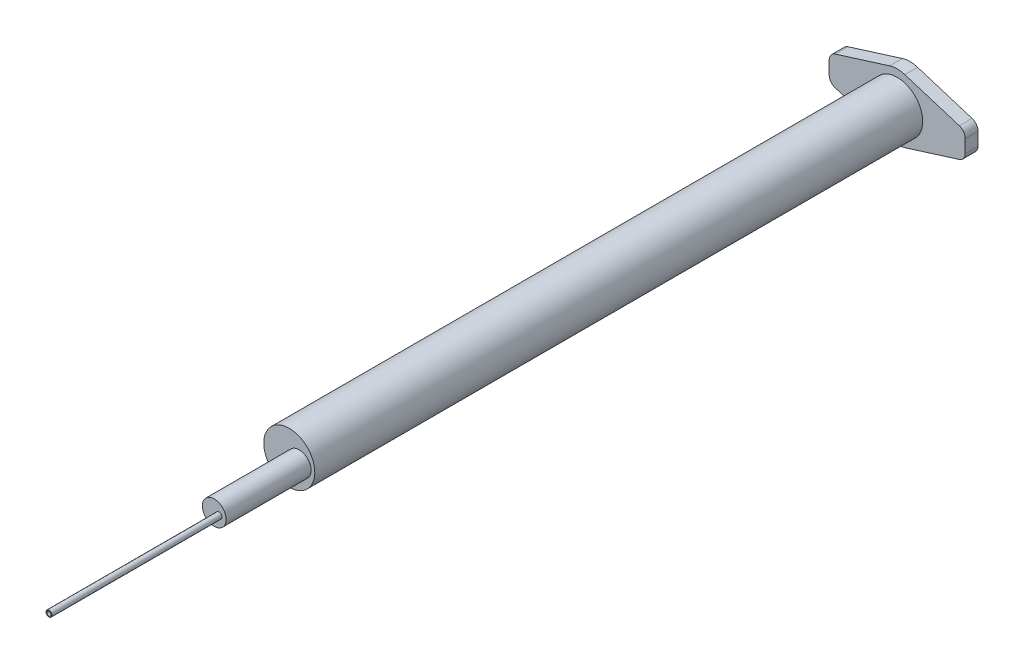
SolidWorks part; units mm, degrees
ref_plane "Front" through (0, 0, 0) normal (0, 0, 1) x (1, 0, 0)
ref_plane "Top" through (0, 0, 0) normal (0, 1, 0) x (1, 0, 0)
ref_plane "Right" through (0, 0, 0) normal (1, 0, 0) x (0, 0, -1)
sketch "草图1" plane through (0, 0, 0) normal (0, 0, 1) x (1, 0, 0)
  circle A0 centre (0, 0) radius 3
  circle A1 centre (0, 0) radius 2.5
extrude "凸台-拉伸1" add sketch "草图1" along normal blind 71.5
sketch "草图2" plane through (0, 0, 71.5) normal (0, 0, 1) x (1, 0, 0)
  circle A0 centre (0, 0) radius 3
  circle A1 centre (1.174, 0) radius 1
  point P5 (1.174, 0)
extrude "凸台-拉伸2" add sketch "草图2" against normal blind 1
sketch "草图3" plane through (0, 0, 0) normal (0, 0, -1) x (-1, 0, 0)
  line L6 (7.2983, -1.7193) -> (0.8948, -3.7204)
  line L7 (-8, 0.7648) -> (-8, 0)
  line L8 (-8, 0) -> (-8, -0.7648)
  line L9 (-7.2983, 1.7193) -> (-0.8948, 3.7204)
  line L10 (-7.2983, -1.7193) -> (-0.8948, -3.7204)
  line L11 (7.2983, 1.7193) -> (0.8948, 3.7204)
  line L12 (8, 0) -> (8, -0.7648)
  line L13 (8, 0.7648) -> (8, 0)
  arc A7 (-7.2983, -1.7193) -> (-8, -0.7648) centre (-7, -0.7648) cw
  arc A8 (-8, 0.7648) -> (-7.2983, 1.7193) centre (-7, 0.7648) cw
  arc A9 (8, 0.7648) -> (7.2983, 1.7193) centre (7, 0.7648) ccw
  arc A10 (7.2983, -1.7193) -> (8, -0.7648) centre (7, -0.7648) ccw
  arc A11 (0.8948, -3.7204) -> (-0.8948, -3.7204) centre (0, -0.8569) cw
  arc A12 (0.8948, 3.7204) -> (-0.8948, 3.7204) centre (0, 0.8569) ccw
  circle A13 centre (0, 0) radius 2.5
  dimension "D1" = 1
  dimension "D2" = 3
extrude "凸台-拉伸3" add sketch "草图3" along normal blind 1.5
sketch "草图4" plane through (0, 0, 71.5) normal (0, 0, 1) x (1, 0, 0)
  circle A0 centre (1.174, 0) radius 1
  circle A1 centre (1.174, 0) radius 1.4
extrude "凸台-拉伸4" add sketch "草图4" along normal blind 9
sketch "草图5" plane through (0, 0, 80.5) normal (0, 0, 1) x (1, 0, 0)
  circle A0 centre (1.174, 0) radius 1.4
  circle A1 centre (1.7404, 0) radius 0.25
extrude "凸台-拉伸5" add sketch "草图5" along normal blind 1
sketch "草图6" plane through (0, 0, 81.5) normal (0, 0, 1) x (1, 0, 0)
  circle A0 centre (1.7404, 0) radius 0.25
  circle A1 centre (1.7404, 0) radius 0.35
extrude "凸台-拉伸6" add sketch "草图6" along normal blind 20
